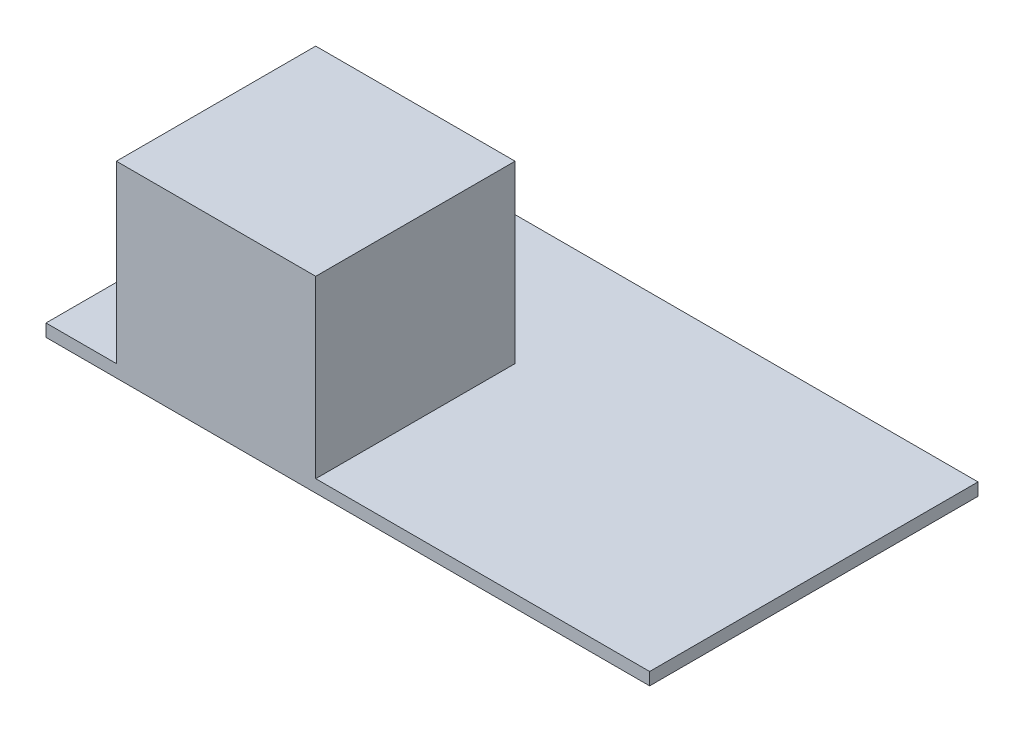
SolidWorks part; units mm, degrees
ref_plane "Front Plane" through (0, 0, 0) normal (0, 0, 1) x (1, 0, 0)
ref_plane "Top Plane" through (0, 0, 0) normal (0, 1, 0) x (1, 0, 0)
ref_plane "Right Plane" through (0, 0, 0) normal (1, 0, 0) x (0, 0, -1)
sketch "Sketch1" plane through (0, 0, 0) normal (0, 1, 0) x (1, 0, 0)
  line L1 (-38.605, 21) -> (38.605, 21)
  line L2 (-38.605, 21) -> (-38.605, -21)
  line L3 (-38.605, -21) -> (38.605, -21)
  line L4 (38.605, 21) -> (38.605, -21)
  line L5 (-38.605, 21) -> (38.605, -21) construction
  line L6 (-38.605, -21) -> (38.605, 21) construction
  point P0 (0, 0)
  dimension "D1" = 77.21
  dimension "D2" = 42
extrude "Boss-Extrude1" add sketch "Sketch1" along normal blind 1.6
sketch "Sketch2" plane through (0, 1.6, 0) normal (0, 1, 0) x (1, 0, 0)
  line L0 (-38.605, 21) -> (-38.605, -21) construction
  line L1 (-29.605, -21) -> (-4.105, -21)
  line L2 (-29.605, -21) -> (-29.605, 4.5)
  line L3 (-29.605, 4.5) -> (-4.105, 4.5)
  line L4 (-4.105, -21) -> (-4.105, 4.5)
  line L5 (-38.605, -21) -> (38.605, -21) construction
  dimension "D1" = 25.5
  dimension "D2" = 25.5
  dimension "D3" = 9
  dimension "D4" = 0
extrude "Boss-Extrude2" add sketch "Sketch2" along normal blind 22.42
